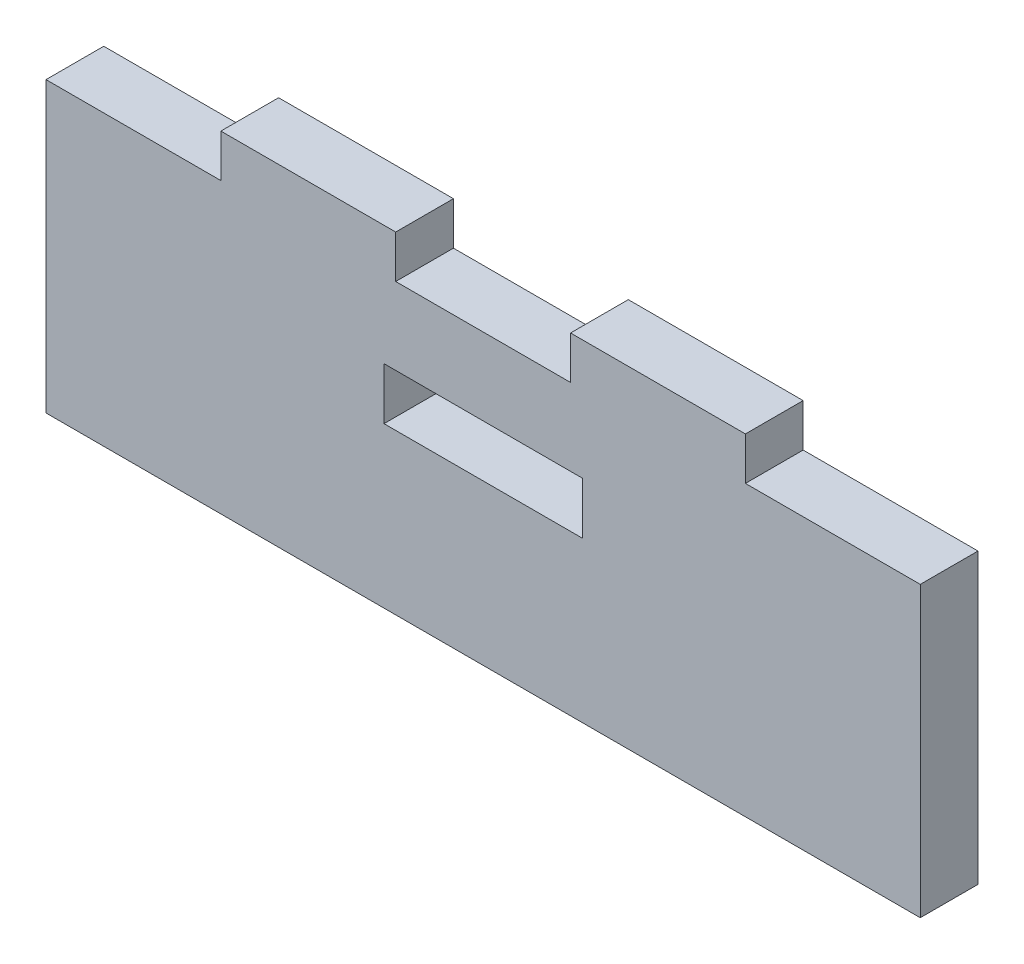
SolidWorks part; units mm, degrees
material "Pino"
ref_plane "Alzado" through (0, 0, 0) normal (0, 0, 1) x (1, 0, 0)
ref_plane "Planta" through (0, 0, 0) normal (0, 1, 0) x (1, 0, 0)
ref_plane "Vista lateral" through (0, 0, 0) normal (1, 0, 0) x (0, 0, -1)
sketch "Croquis1" plane through (0, 0, 0) normal (0, 0, 1) x (1, 0, 0)
  line L0 (10.7938, 10.7357) -> (19.8778, 10.7357)
  line L1 (-25.5422, 10.7357) -> (-16.4582, 10.7357)
  line L2 (-25.5422, 10.7357) -> (-25.5422, -4.2643)
  line L3 (-25.5422, -4.2643) -> (19.8778, -4.2643)
  line L4 (19.8778, 10.7357) -> (19.8778, -4.2643)
  line L5 (-7.9822, 6.7357) -> (2.3178, 6.7357)
  line L6 (-7.9822, 6.7357) -> (-7.9822, 4.0357)
  line L7 (-7.9822, 4.0357) -> (2.3178, 4.0357)
  line L8 (2.3178, 6.7357) -> (2.3178, 4.0357)
  line L12 (-16.4582, 10.7357) -> (-16.4582, 12.9621)
  line L13 (-7.3742, 10.7357) -> (1.7098, 10.7357)
  line L14 (-7.3742, 10.7357) -> (-7.3742, 12.9621)
  line L16 (1.7098, 10.7357) -> (1.7098, 12.9621)
  line L20 (10.7938, 10.7357) -> (10.7938, 12.9621)
  line L21 (10.7938, 12.9621) -> (1.7098, 12.9621)
  line L25 (-7.3742, 12.9621) -> (-16.4582, 12.9621)
  dimension "D1" = 45.42
  dimension "D2" = 15
  dimension "D3" = 2.7
  dimension "D4" = 10.3
  dimension "D5" = 4
  dimension "D6" = 17.56
  dimension "D8" = 9.084
  dimension "D9" = 9.084
  dimension "D10" = 9.084
extrude "Saliente-Extruir1" add sketch "Croquis1" along normal blind 3
